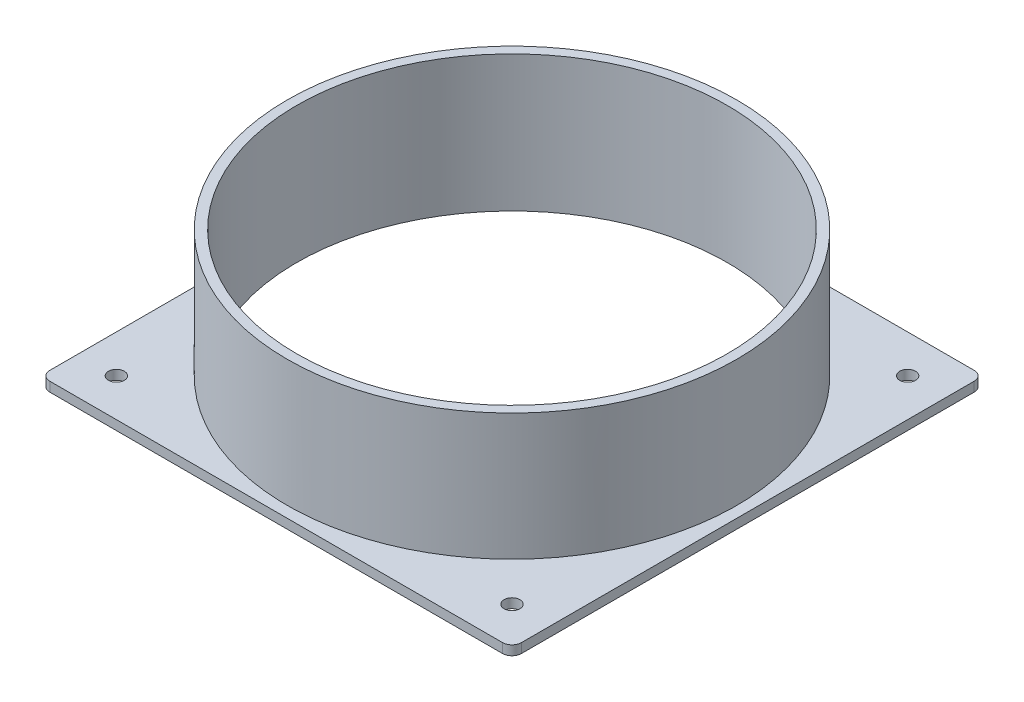
SolidWorks part; units mm, degrees
ref_plane "Front Plane" through (0, 0, 0) normal (0, 0, 1) x (1, 0, 0)
ref_plane "Top Plane" through (0, 0, 0) normal (0, 1, 0) x (1, 0, 0)
ref_plane "Right Plane" through (0, 0, 0) normal (1, 0, 0) x (0, 0, -1)
sketch "Sketch4" plane through (0, 0, 0) normal (0, 1, 0) x (1, 0, 0)
  line L0 (0, 74.5) -> (0, -74.5) construction
  line L1 (-71.5, 74.5) -> (71.5, 74.5)
  line L2 (-74.5, 71.5) -> (-74.5, -71.5)
  line L3 (-71.5, -74.5) -> (71.5, -74.5)
  line L4 (74.5, 71.5) -> (74.5, -71.5)
  line L5 (-74.5, 74.5) -> (74.5, -74.5) construction
  line L6 (-74.5, -74.5) -> (74.5, 74.5) construction
  line L7 (-74.5, 0) -> (74.5, 0) construction
  arc A0 (-71.5, -74.5) -> (-74.5, -71.5) centre (-71.5, -71.5) cw
  arc A1 (71.5, -74.5) -> (74.5, -71.5) centre (71.5, -71.5) ccw
  arc A2 (74.5, 71.5) -> (71.5, 74.5) centre (71.5, 71.5) ccw
  arc A3 (-71.5, 74.5) -> (-74.5, 71.5) centre (-71.5, 71.5) ccw
  circle A4 centre (0, 0) radius 68
  circle A5 centre (-62.5, 62.5) radius 2.5
  circle A6 centre (62.5, 62.5) radius 2.5
  circle A7 centre (62.5, -62.5) radius 2.5
  circle A8 centre (-62.5, -62.5) radius 2.5
  point P0 (0, 0)
  point P35 (0, 0)
  dimension "D3" = 3
  dimension "D4" = 62.5
  dimension "D1" = 149
  dimension "D2" = 149
  dimension "D5" = 62.5
  dimension "D6" = 4
extrude "Boss-Extrude5" add sketch "Sketch4" along normal blind 3
sketch "Sketch5" plane through (0, 3, 0) normal (0, 1, 0) x (1, 0, 0)
  circle A0 centre (0, 0) radius 68
  circle A1 centre (0, 0) radius 71
  dimension "D1" = 3
extrude "Boss-Extrude6" add sketch "Sketch5" along normal blind 40
